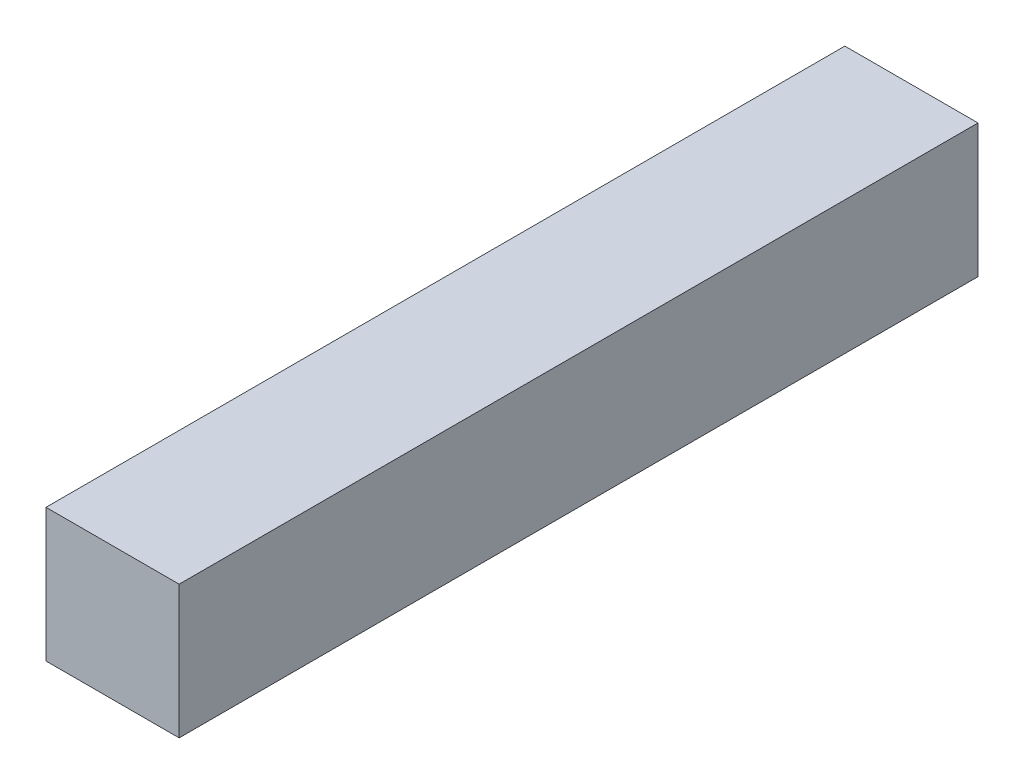
SolidWorks part; units mm, degrees
ref_plane "Front Plane" through (0, 0, 0) normal (0, 0, 1) x (1, 0, 0)
ref_plane "Top Plane" through (0, 0, 0) normal (0, 1, 0) x (1, 0, 0)
ref_plane "Right Plane" through (0, 0, 0) normal (1, 0, 0) x (0, 0, -1)
sketch "Sketch1" plane through (0, 0, 0) normal (0, 0, 1) x (1, 0, 0)
  line L1 (25, -25) -> (-25, -25)
  line L2 (25, -25) -> (25, 25)
  line L3 (25, 25) -> (-25, 25)
  line L4 (-25, -25) -> (-25, 25)
  line L5 (25, -25) -> (-25, 25) construction
  line L6 (25, 25) -> (-25, -25) construction
  point P0 (0, 0)
  dimension "D1" = 50
  dimension "D2" = 50
extrude "Boss-Extrude1" add sketch "Sketch1" along normal blind 300
